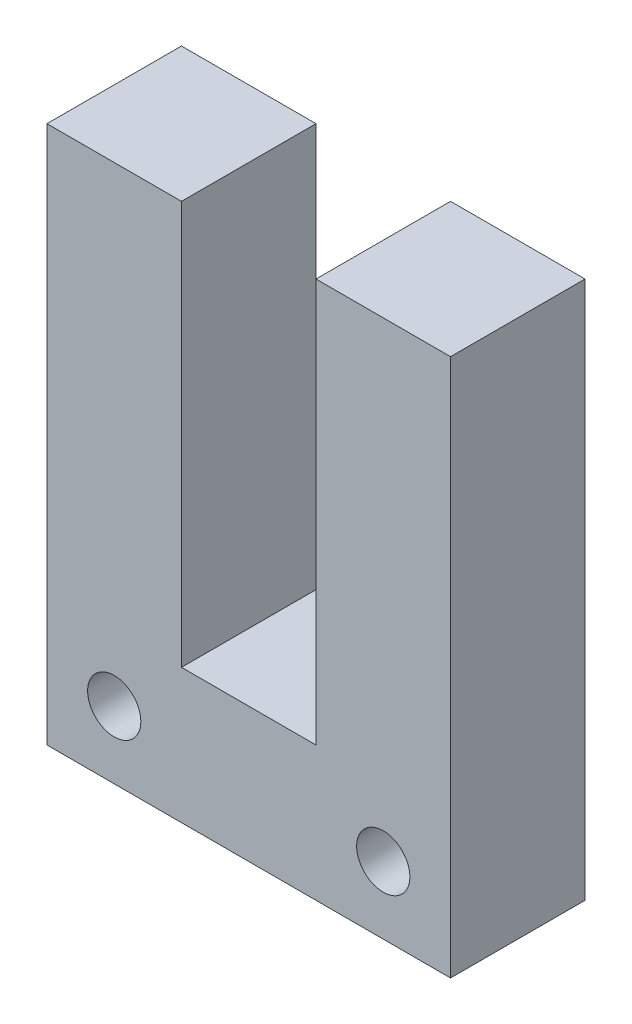
SolidWorks part; units mm, degrees
material "6061 Alloy"
ref_plane "Front Plane" through (0, 0, 0) normal (0, 0, 1) x (1, 0, 0)
ref_plane "Top Plane" through (0, 0, 0) normal (0, 1, 0) x (1, 0, 0)
ref_plane "Right Plane" through (0, 0, 0) normal (1, 0, 0) x (0, 0, -1)
sketch "Sketch1" plane through (0, 0, 0) normal (0, 0, 1) x (1, 0, 0)
  line L1 (0, 0) -> (19.05, 0)
  line L2 (0, 0) -> (0, 25.4)
  line L3 (0, 25.4) -> (19.05, 25.4)
  line L4 (19.05, 0) -> (19.05, 25.4)
  dimension "D1" = 19.05
  dimension "D2" = 25.4
extrude "Main block" add sketch "Sketch1" along normal blind 6.35
sketch "Sketch2" plane through (0, 0, 6.35) normal (0, 0, 1) x (1, 0, 0)
  line L0 (19.05, 25.4) -> (0, 25.4) construction
  line L1 (6.35, 6.35) -> (12.7, 6.35)
  line L2 (6.35, 6.35) -> (6.35, 25.4)
  line L3 (6.35, 25.4) -> (12.7, 25.4)
  line L4 (12.7, 6.35) -> (12.7, 25.4)
  line L6 (19.05, 0) -> (19.05, 25.4) construction
  dimension "D1" = 6.35
  dimension "D2" = 6.35
  dimension "D3" = 19.05
extrude "U-cut" cut sketch "Sketch2" against normal blind 12.7
sketch "Sketch3" plane through (0, 0, 6.35) normal (0, 0, 1) x (1, 0, 0)
  line L0 (0, 0) -> (19.05, 0) construction
  line L1 (19.05, 0) -> (19.05, 25.4) construction
  line L2 (0, 25.4) -> (0, 0) construction
  circle A0 centre (3.175, 3.175) radius 1.256
  circle A1 centre (15.875, 3.175) radius 1.256
  dimension "D3" = 2.5121
  dimension "D4" = 2.5121
  dimension "D1" = 3.175
  dimension "D2" = 3.175
  dimension "D5" = 3.175
  dimension "D6" = 3.175
extrude "Bolt holes" cut sketch "Sketch3" against normal blind 12.7
